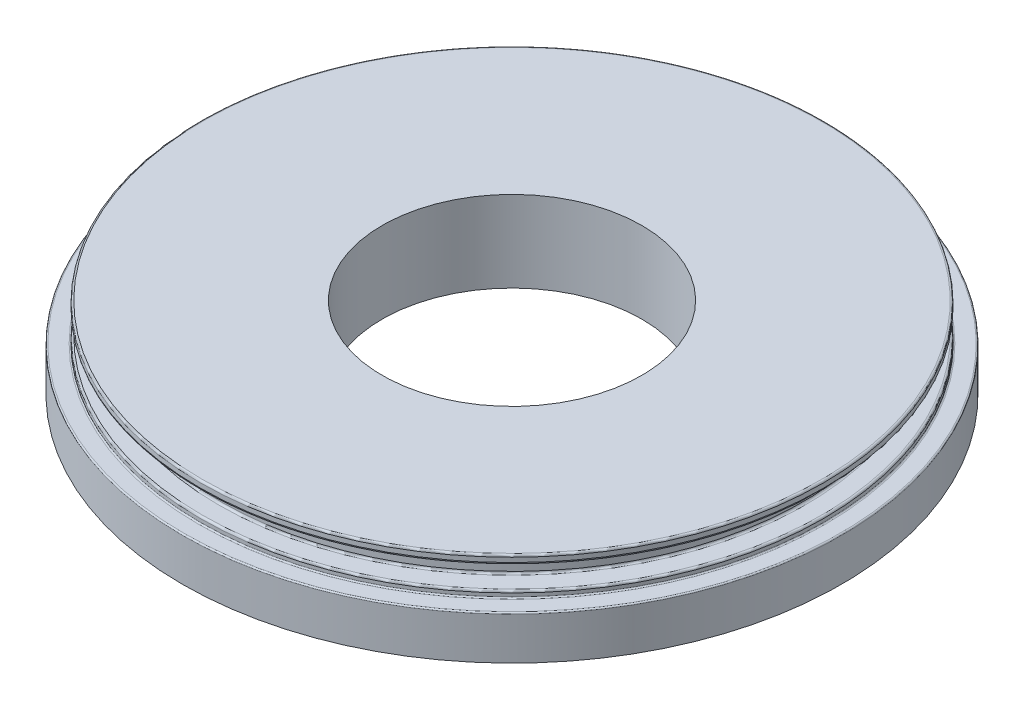
SolidWorks part; units mm, degrees
ref_plane "Front Plane" through (0, 0, 0) normal (0, 0, 1) x (1, 0, 0)
ref_plane "Top Plane" through (0, 0, 0) normal (0, 1, 0) x (1, 0, 0)
ref_plane "Right Plane" through (0, 0, 0) normal (1, 0, 0) x (0, 0, -1)
sketch "Sketch1" plane through (0, 0, 0) normal (0, 0, 1) x (1, 0, 0)
  line L0 (0, 0) -> (0, 6.38)
  line L1 (9.93, 0) -> (25.2, 0)
  line L2 (25.2, 0) -> (25.2, 3.34)
  line L3 (25.2, 3.34) -> (23.8456, 3.34)
  line L4 (23.8456, 3.34) -> (23.8456, 3.84)
  line L5 (22.25, 5.5543) -> (23.8456, 5.5543)
  line L6 (23.8456, 5.5543) -> (23.8456, 6.2043)
  line L7 (23.8456, 6.2043) -> (9.93, 6.2043)
  line L8 (23.8456, 3.84) -> (22.25, 3.84)
  line L9 (22.25, 3.84) -> (22.25, 5.5543)
  line L11 (9.93, 0) -> (9.93, 6.2043)
  dimension "D1" = 25.2
  dimension "D2" = 6.38
  dimension "D3" = 2.95
  dimension "D4" = 3.34
  dimension "D5" = 6.2043
  dimension "D6" = 9.93
  dimension "D7" = 0.5
  dimension "D8" = 0
  dimension "D9" = 0.65
revolve "Revolve1" add sketch "Sketch1" angle 360 about L0
fillet "Fillet2" radius 0.15 1 edges at (0, 6.2043, -23.8456)
fillet "Fillet3" radius 0.15 2 edges at (0, 3.84, -23.8456) (0, 5.5543, -23.8456)
fillet "Fillet4" radius 0.1 2 edges at (0, 3.34, -25.2) (0, 3.34, -23.8456)
fillet "Fillet5" radius 0.15 1 edges at (0, 3.84, -22.25)
fillet "Fillet6" radius 0.15 1 edges at (0, 5.5543, -22.25)
